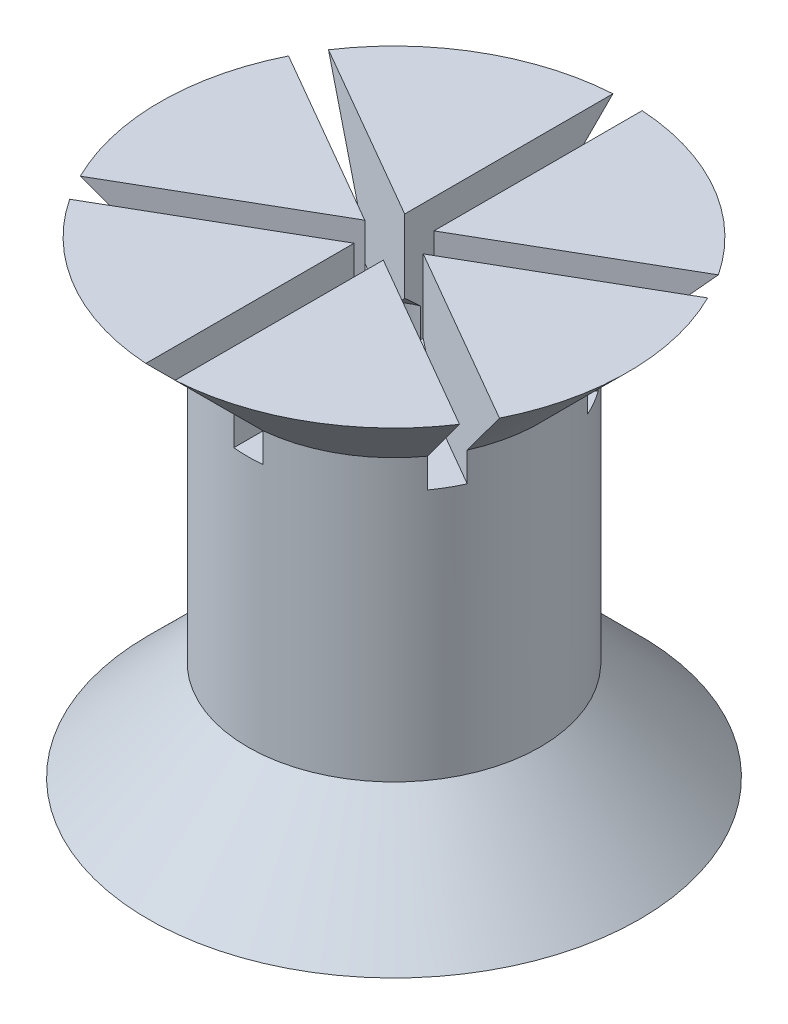
SolidWorks part; units mm, degrees
ref_plane "前视基准面" through (0, 0, 0) normal (0, 0, 1) x (1, 0, 0)
ref_plane "上视基准面" through (0, 0, 0) normal (0, 1, 0) x (1, 0, 0)
ref_plane "右视基准面" through (0, 0, 0) normal (1, 0, 0) x (0, 0, -1)
other "Configuration Table"
sketch "草图1" plane through (0, 0, 0) normal (0, 0, 1) x (1, 0, 0)
  line L0 (-90.2815, -4) -> (141.0397, -4) construction
  line L1 (-160.9179, 0) -> (191.7291, 0) construction
  line L2 (112.8607, 0) -> (-112.8607, 0) construction
  line L3 (-90.5, -4) -> (-89.5, -4) construction
  line L4 (-19.471, -16) -> (20.0064, -16) construction
  line L6 (-2.7, -16) -> (-0.2, -16) construction
  line L7 (0, 34.9193) -> (0, -36.3797) construction
ref_plane "基准面1" through (0, -16, 0) normal (0, -1, 0) x (-1, 0, 0)
sketch "草图2" plane through (0, -16, 0) normal (0, -1, 0) x (-1, 0, 0)
  line L1 (0, 3.0022) -> (-2.6, 1.5011)
  line L2 (-2.6, 1.5011) -> (-2.6, -1.5011)
  line L3 (-2.6, -1.5011) -> (0, -3.0022)
  line L4 (0, -3.0022) -> (2.6, -1.5011)
  line L5 (2.6, -1.5011) -> (2.6, 1.5011)
  line L6 (2.6, 1.5011) -> (0, 3.0022)
  circle A0 centre (0, 0) radius 2.6 construction
  circle A1 centre (0, 0) radius 10
  dimension "D1" = 5.2
  dimension "D2" = 20
extrude "凸台-拉伸1" add sketch "草图2" against normal blind 3.4
sketch "草图5" plane through (0, 0, 0) normal (0, 0, 1) x (1, 0, 0)
  line L0 (0, 22.9281) -> (0, -29.1186) construction
  line L1 (0, -12.6) -> (-5, -12.6)
  line L2 (10, -12.6) -> (-10, -12.6) construction
  line L3 (-5, -12.6) -> (-5, -4)
  line L4 (-90.2815, -4) -> (141.0397, -4) construction
  line L5 (-5, -4) -> (0, -4)
  line L6 (0, -4) -> (0, -12.6)
  dimension "D1" = 5
revolve "旋转1" add sketch "草图5" angle 360 about L0
sketch "草图6" plane through (0, 0, 0) normal (0, 0, 1) x (1, 0, 0)
  line L0 (-5, -12.6) -> (-10, -17.6)
  line L1 (-10, -17.6) -> (-10, -12.6)
  line L2 (-10, -12.6) -> (-5, -12.6)
  line L3 (-10, -12.6) -> (-10, -16) construction
  line L4 (0, 0) -> (0, -8.1317) construction
  line L5 (0, -12.6) -> (0, -16) construction
  dimension "D1" = 45
revolve "切除-旋转1" cut sketch "草图6" angle 360 about L4
sketch "草图7" plane through (0, 0, 0) normal (0, 0, 1) x (1, 0, 0)
  line L0 (0, 2.9015) -> (0, -11.8033) construction
  line L1 (-5, -4) -> (0, -4)
  line L2 (-90.2815, -4) -> (141.0397, -4) construction
  line L3 (-5, -4) -> (-5, -12.6) construction
  line L4 (0, -4) -> (0, 0)
  line L5 (0, 0) -> (-8, 0)
  line L6 (-8, 0) -> (-5, -3)
  line L7 (-5, -3) -> (-5, -4)
  line L8 (-160.9179, 0) -> (191.7291, 0) construction
  line L9 (0, 34.9193) -> (0, -36.3797) construction
  dimension "D1" = 1
  dimension "D2" = 135
revolve "旋转2" add sketch "草图7" angle 360 about L0
sketch "草图8" plane through (0, 0, 0) normal (1, 0, 0) x (0, 0, -1)
  line L1 (0, 34.9193) -> (0, -36.3797) construction
  line L3 (-5, -3) -> (-8, 0)
  line L4 (-8, 0) -> (0, 0)
  line L5 (0, 5.2492) -> (0, -15.6726) construction
  line L6 (-5, -3) -> (-5, -4)
  line L7 (-5, -3) -> (-5, -12.6) construction
  line L8 (-5, -4) -> (0, -4)
  line L14 (0, 0) -> (0, -4)
  dimension "D1" = 1
extrude "切除-拉伸1" cut sketch "草图8" against normal mid plane 1
pattern_circular "阵列(圆周)1" count 6 over 360 about axis through (0, 0, 0) along (0, 1, 0) of "切除-拉伸1"
sketch "草图9" plane through (0, 0, 0) normal (0, 0, 1) x (1, 0, 0)
  line L0 (0, 4.4895) -> (0, -10.3567) construction
  line L1 (0, 34.9193) -> (0, -36.3797) construction
  line L2 (0, -4) -> (-1.5, -4)
  line L3 (-90.2815, -4) -> (141.0397, -4) construction
  line L4 (-1.5, -4) -> (-1.5, -3)
  line L5 (-4.0584, -3) -> (-0.5, -3) construction
  line L6 (-1.5, -3) -> (0, -1.5)
  line L7 (0, -1.5) -> (0, -4)
  line L9 (-1, 0) -> (-1, -4) construction
  dimension "D1" = 0.5
  dimension "D2" = 45
revolve "切除-旋转3" cut sketch "草图9" angle 360 about L0
fillet "圆角4" [suppressed] radius 0.3
